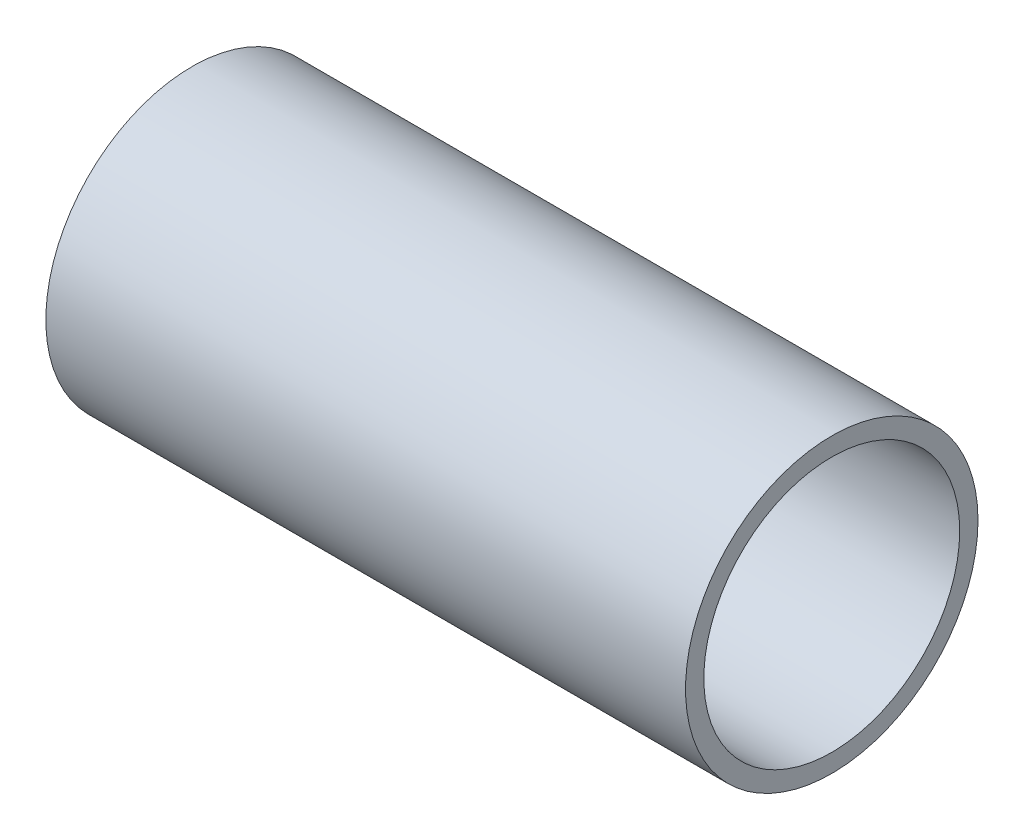
SolidWorks part; units mm, degrees
material "Wildman Fiberglass"
ref_plane "Front Plane" through (0, 0, 0) normal (0, 0, 1) x (1, 0, 0)
ref_plane "Top Plane" through (0, 0, 0) normal (0, 1, 0) x (1, 0, 0)
ref_plane "Right Plane" through (0, 0, 0) normal (1, 0, 0) x (0, 0, -1)
sketch "Sketch1" plane through (0, 0, 0) normal (1, 0, 0) x (0, 0, -1)
  circle A0 centre (0, 0) radius 14.5161
  circle A1 centre (0, 0) radius 12.7
  dimension "D1" = 25.4
  dimension "D2" = 29.0322
extrude "Boss-Extrude1" add sketch "Sketch1" along normal mid plane 63.5
